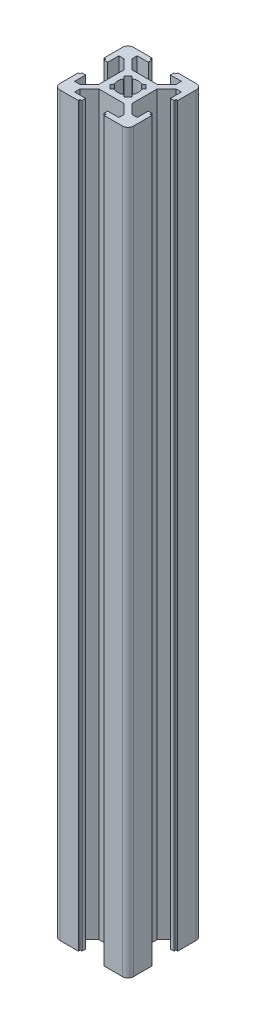
SolidWorks part; units mm, degrees
material "3.3547 (EN-AW 5083)"
ref_plane "Płaszczyzna przednia" through (0, 0, 0) normal (0, 0, 1) x (1, 0, 0)
ref_plane "Płaszczyzna górna" through (0, 0, 0) normal (0, 1, 0) x (1, 0, 0)
ref_plane "Płaszczyzna prawa" through (0, 0, 0) normal (1, 0, 0) x (0, 0, -1)
sketch "Szkic1" plane through (0, 0, 0) normal (0, 1, 0) x (1, 0, 0)
  line L0 (0, 10) -> (0, -10) construction
  line L1 (4.5, -4.5) -> (-4.5, -4.5)
  line L2 (4.5, -4.5) -> (4.5, 4.5)
  line L3 (4.5, 4.5) -> (-4.5, 4.5)
  line L4 (-4.5, -4.5) -> (-4.5, 4.5)
  line L5 (4.5, -4.5) -> (-4.5, 4.5) construction
  line L6 (4.5, 4.5) -> (-4.5, -4.5) construction
  line L7 (8.5, -10) -> (-8.5, -10)
  line L8 (10, -8.5) -> (10, 8.5)
  line L9 (8.5, 10) -> (-8.5, 10)
  line L10 (-10, -8.5) -> (-10, 8.5)
  line L11 (10, -10) -> (-10, 10) construction
  line L12 (10, 10) -> (-10, -10) construction
  line L13 (3.5, 10) -> (-3.5, 10)
  line L14 (-3.5, 10) -> (-3.5, 9.5)
  line L15 (-3.5, 9.5) -> (-3, 9.5)
  line L16 (-3, 9.5) -> (-3, 8.5)
  line L17 (-3, 8.5) -> (-6, 8.5)
  line L18 (-6, 8.5) -> (-6, 7.06)
  line L19 (-6, 7.06) -> (-3.4405, 4.5)
  line L20 (-1.9445, 3.0052) -> (-3.0052, 1.9445)
  line L21 (-1.9445, 3.0052) -> (-1.2713, 2.4385)
  line L22 (-3.0052, 1.9445) -> (-2.4385, 1.2713)
  line L23 (3.5, 10) -> (3.5, 9.5)
  line L24 (3.5, 9.5) -> (3, 9.5)
  line L25 (3, 9.5) -> (3, 8.5)
  line L26 (3, 8.5) -> (6, 8.5)
  line L27 (6, 8.5) -> (6, 7.06)
  line L28 (6, 7.06) -> (3.4405, 4.5)
  line L29 (1.9445, 3.0052) -> (3.0052, 1.9445)
  line L30 (1.9445, 3.0052) -> (1.2713, 2.4385)
  line L31 (3.0052, 1.9445) -> (2.4385, 1.2713)
  line L32 (1.9445, 3.0052) -> (1.2713, 2.4385)
  line L33 (3.0052, 1.9445) -> (1.9445, 3.0052)
  line L34 (3.0052, 1.9445) -> (2.4385, 1.2713)
  line L35 (7.06, 6) -> (4.5, 3.4405)
  line L36 (8.5, 6) -> (7.06, 6)
  line L37 (8.5, 3) -> (8.5, 6)
  line L38 (9.5, 3) -> (8.5, 3)
  line L39 (9.5, 3.5) -> (9.5, 3)
  line L40 (10, 3.5) -> (9.5, 3.5)
  line L41 (10, -3.5) -> (9.5, -3.5)
  line L42 (9.5, -3.5) -> (9.5, -3)
  line L43 (9.5, -3) -> (8.5, -3)
  line L44 (8.5, -3) -> (8.5, -6)
  line L45 (8.5, -6) -> (7.06, -6)
  line L46 (7.06, -6) -> (4.5, -3.4405)
  line L47 (3.0052, -1.9445) -> (2.4385, -1.2713)
  line L48 (3.0052, -1.9445) -> (1.9445, -3.0052)
  line L49 (1.9445, -3.0052) -> (1.2713, -2.4385)
  line L50 (3.0052, -1.9445) -> (2.4385, -1.2713)
  line L51 (1.9445, -3.0052) -> (3.0052, -1.9445)
  line L52 (1.9445, -3.0052) -> (1.2713, -2.4385)
  line L53 (6, -7.06) -> (3.4405, -4.5)
  line L54 (6, -8.5) -> (6, -7.06)
  line L55 (3, -8.5) -> (6, -8.5)
  line L56 (3, -9.5) -> (3, -8.5)
  line L57 (3.5, -9.5) -> (3, -9.5)
  line L58 (3.5, -10) -> (3.5, -9.5)
  line L59 (-3.5, -10) -> (-3.5, -9.5)
  line L60 (-3.5, -9.5) -> (-3, -9.5)
  line L61 (-3, -9.5) -> (-3, -8.5)
  line L62 (-3, -8.5) -> (-6, -8.5)
  line L63 (-6, -8.5) -> (-6, -7.06)
  line L64 (-6, -7.06) -> (-3.4405, -4.5)
  line L65 (-1.9445, -3.0052) -> (-1.2713, -2.4385)
  line L66 (-1.9445, -3.0052) -> (-3.0052, -1.9445)
  line L67 (-3.0052, -1.9445) -> (-2.4385, -1.2713)
  line L68 (-1.9445, -3.0052) -> (-1.2713, -2.4385)
  line L69 (-3.0052, -1.9445) -> (-1.9445, -3.0052)
  line L70 (-3.0052, -1.9445) -> (-2.4385, -1.2713)
  line L71 (-7.06, -6) -> (-4.5, -3.4405)
  line L72 (-8.5, -6) -> (-7.06, -6)
  line L73 (-8.5, -3) -> (-8.5, -6)
  line L74 (-9.5, -3) -> (-8.5, -3)
  line L75 (-9.5, -3.5) -> (-9.5, -3)
  line L76 (-10, -3.5) -> (-9.5, -3.5)
  line L77 (-10, 3.5) -> (-9.5, 3.5)
  line L78 (-9.5, 3.5) -> (-9.5, 3)
  line L79 (-9.5, 3) -> (-8.5, 3)
  line L80 (-8.5, 3) -> (-8.5, 6)
  line L81 (-8.5, 6) -> (-7.06, 6)
  line L82 (-7.06, 6) -> (-4.5, 3.4405)
  line L83 (-3.0052, 1.9445) -> (-2.4385, 1.2713)
  line L84 (-3.0052, 1.9445) -> (-1.9445, 3.0052)
  line L85 (-1.9445, 3.0052) -> (-1.2713, 2.4385)
  circle A0 centre (0, 0) radius 2.75
  arc A1 (10, -8.5) -> (8.5, -10) centre (8.5, -8.5) cw
  arc A2 (-10, -8.5) -> (-8.5, -10) centre (-8.5, -8.5) ccw
  arc A3 (10, 8.5) -> (8.5, 10) centre (8.5, 8.5) ccw
  arc A4 (-8.5, 10) -> (-10, 8.5) centre (-8.5, 8.5) ccw
  point P16 (0, 10)
  point P37 (-2.4749, 2.4749)
  dimension "D1" = 5.5
  dimension "D12" = 1.5
  dimension "D2" = 9
  dimension "D3" = 20
  dimension "D4" = 20
  dimension "D5" = 7
  dimension "D6" = 0.5
  dimension "D7" = 0.5
  dimension "D8" = 1
  dimension "D9" = 3
  dimension "D10" = 1.44
  dimension "D11" = 3.62
  dimension "D13" = 1.5
  dimension "D14" = 3.5
  dimension "D15" = 0.88
  dimension "D16" = 4
extrude "Dodanie-wyciągnięcie1" add sketch "Szkic1" along normal blind 807 contours L9 A4 L10 L77 L78 L79 L80 L81 L82 L4 L3 L19 L18 L17 L16 L15 L14 | L8 A3 L9 L23 L24 L25 L26 L27 L28 L3 L2 L35 L36 L37 L38 L39 L40 | L4 L1 L2 L3 A0 L47 L48 L49 L65 L66 L67 L22 L20 L21 L30 L29 L31 | L10 A2 L7 L59 L60 L61 L62 L63 L64 L1 L4 L71 L72 L73 L74 L75 L76 | A1 L8 L41 L42 L43 L44 L45 L46 L2 L1 L53 L54 L55 L56 L57 L58 L7
sketch "Skizze1" plane through (0, 0, 0) normal (0, 0, 1) x (1, 0, 0)
  line L0 (-83.4963, 200) -> (63.9108, 200)
  line L1 (63.9108, 200) -> (55.1488, 860.7548)
  line L2 (55.1488, 860.7548) -> (-83.4963, 858.9163)
  line L3 (-83.4963, 858.9163) -> (-83.4963, 200)
  dimension "D1" = 200
extrude "Schnitt-Linear austragen1" cut sketch "Skizze1" against normal mid plane 40
other "Freeze***"
